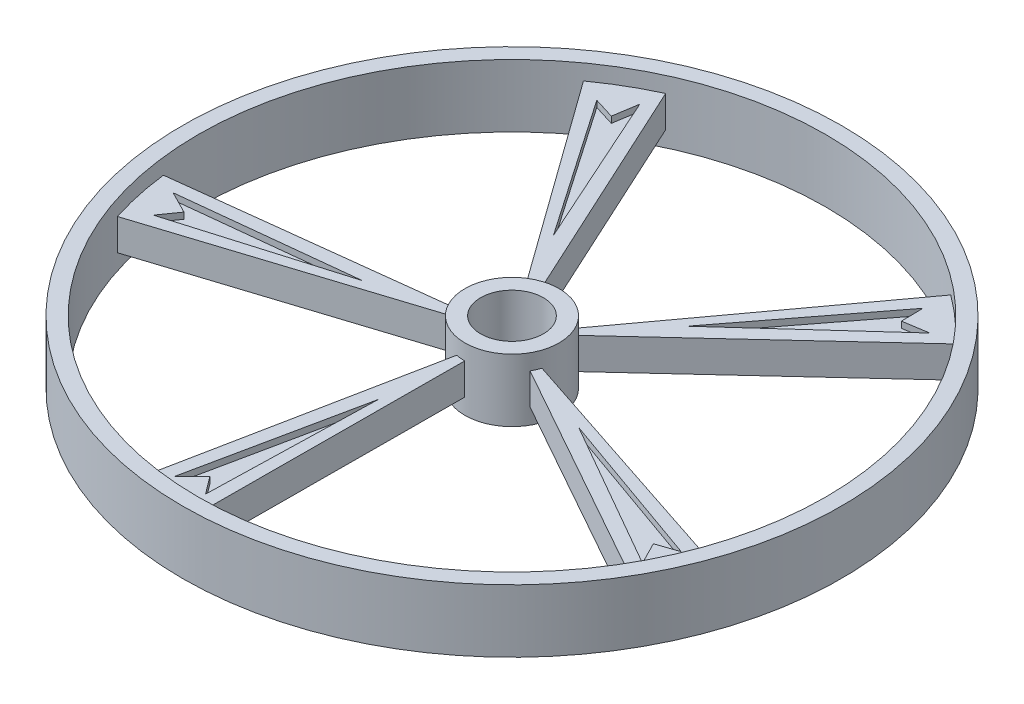
SolidWorks part; units mm, degrees
ref_plane "前视基准面" through (0, 0, 0) normal (0, 0, 1) x (1, 0, 0)
ref_plane "上视基准面" through (0, 0, 0) normal (0, 1, 0) x (1, 0, 0)
ref_plane "右视基准面" through (0, 0, 0) normal (1, 0, 0) x (0, 0, -1)
sketch "草图1" plane through (0, 0, 0) normal (0, 1, 0) x (1, 0, 0)
  circle A0 centre (0, 0) radius 50
  circle A1 centre (0, 0) radius 75
  dimension "D1" = 100
  dimension "D2" = 150
extrude "凸台-拉伸1" add sketch "草图1" along normal mid plane 100
sketch "草图2" plane through (0, 0, 0) normal (0, 1, 0) x (1, 0, 0)
  circle A0 centre (0, 0) radius 525
  circle A1 centre (0, 0) radius 500
  dimension "D1" = 1000
  dimension "D2" = 1050
extrude "凸台-拉伸2" add sketch "草图2" along normal mid plane 100 separate body
sketch "草图3" plane through (0, 0, 0) normal (0, 1, 0) x (1, 0, 0)
  line L0 (0, 0) -> (487.741, -160.9668)
  line L1 (487.741, -160.9668) -> (449.99, -252.0606)
  line L2 (449.99, -252.0606) -> (0, 0)
  line L3 (-100.6694, -505.8569) -> (0, 0)
  line L4 (0, 0) -> (-2.3683, -513.6107)
  line L6 (-2.3683, -513.6107) -> (-100.6694, -505.8569)
  line L7 (-512.2071, -60.5761) -> (0, 0)
  line L8 (0, 0) -> (-489.2047, -156.4621)
  line L9 (-489.2047, -156.4621) -> (-512.2071, -60.5761)
  line L10 (-215.892, 468.4188) -> (0, 0)
  line L11 (0, 0) -> (-299.9768, 416.9119)
  line L20 (-299.9768, 416.9119) -> (-215.892, 468.4188)
  line L21 (378.7785, 350.0749) -> (0, 0)
  line L22 (0, 0) -> (303.8088, 414.1278)
  line L23 (303.8088, 414.1278) -> (378.7785, 350.0749)
  circle A0 centre (0, 0) radius 50
  dimension "D1" = 100
  dimension "D2" = 5
extrude "凸台-拉伸4" add sketch "草图3" along normal mid plane 50 contours A0 L21 L23 L22 | A0 L2 L1 L0 | A0 L3 L6 L4 | A0 L7 L9 L8 | A0 L10 L20 L11
sketch "草图4" plane through (0, -25, 0) normal (0, -1, 0) x (1, 0, 0)
  line L0 (-72.0524, 465.1667) -> (-44.0408, 437.1552)
  line L1 (-44.0408, 437.1552) -> (-23.0321, 465.1667)
  line L2 (-23.0321, 465.1667) -> (-16.0292, 197.056)
  line L3 (-16.0292, 197.056) -> (-72.0524, 465.1667)
  point P8 (143.0365, 215.0634)
  point P12 (-267.133, 543.199)
extrude "切除-拉伸1" cut sketch "草图4" against normal blind 10
mirror "镜向1" about plane through (0, 0, 0) normal (0, 1, 0) of "切除-拉伸1"
pattern_circular "阵列(圆周)1" count 5 over 360 about axis through (0, 0, 0) along (0, 1, 0) of "镜向1", "切除-拉伸1"
